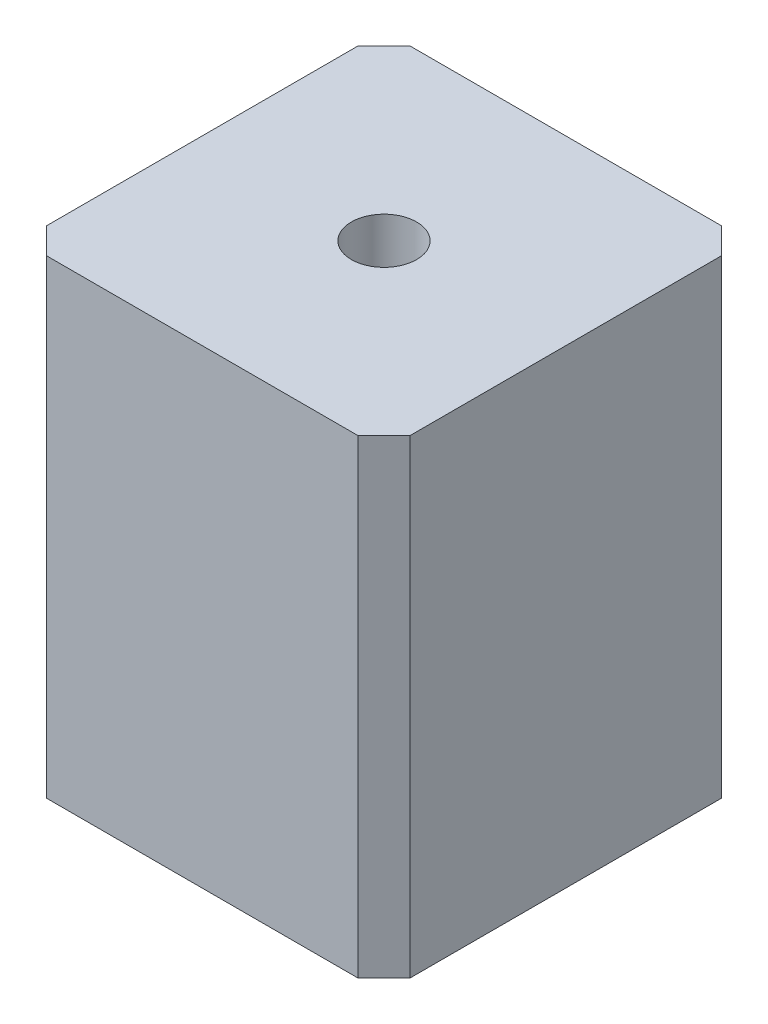
SolidWorks part; units mm, degrees
ref_plane "Спереди" through (0, 0, 0) normal (0, 0, 1) x (1, 0, 0)
ref_plane "Сверху" through (0, 0, 0) normal (0, 1, 0) x (1, 0, 0)
ref_plane "Справа" through (0, 0, 0) normal (1, 0, 0) x (0, 0, -1)
sketch "Эскиз2" plane through (0, 0, 0) normal (0, 1, 0) x (1, 0, 0)
  line L1 (-13.925, -13.925) -> (13.925, -13.925)
  line L2 (-13.925, -13.925) -> (-13.925, 13.925)
  line L3 (-13.925, 13.925) -> (13.925, 13.925)
  line L4 (13.925, -13.925) -> (13.925, 13.925)
  line L5 (-13.925, -13.925) -> (13.925, 13.925) construction
  line L6 (-13.925, 13.925) -> (13.925, -13.925) construction
  circle A0 centre (0, 0) radius 2.5
  point P0 (0, 0)
  dimension "D3" = 27.85
  dimension "D4" = 27.85
extrude "Бобышка-Вытянуть1" add sketch "Эскиз2" along normal blind 36
chamfer "Фаска1" distance 2 angle 45 4 edges at (13.925, 18, 13.925) (-13.925, 18, 13.925) (-13.925, 18, -13.925) (13.925, 18, -13.925)
